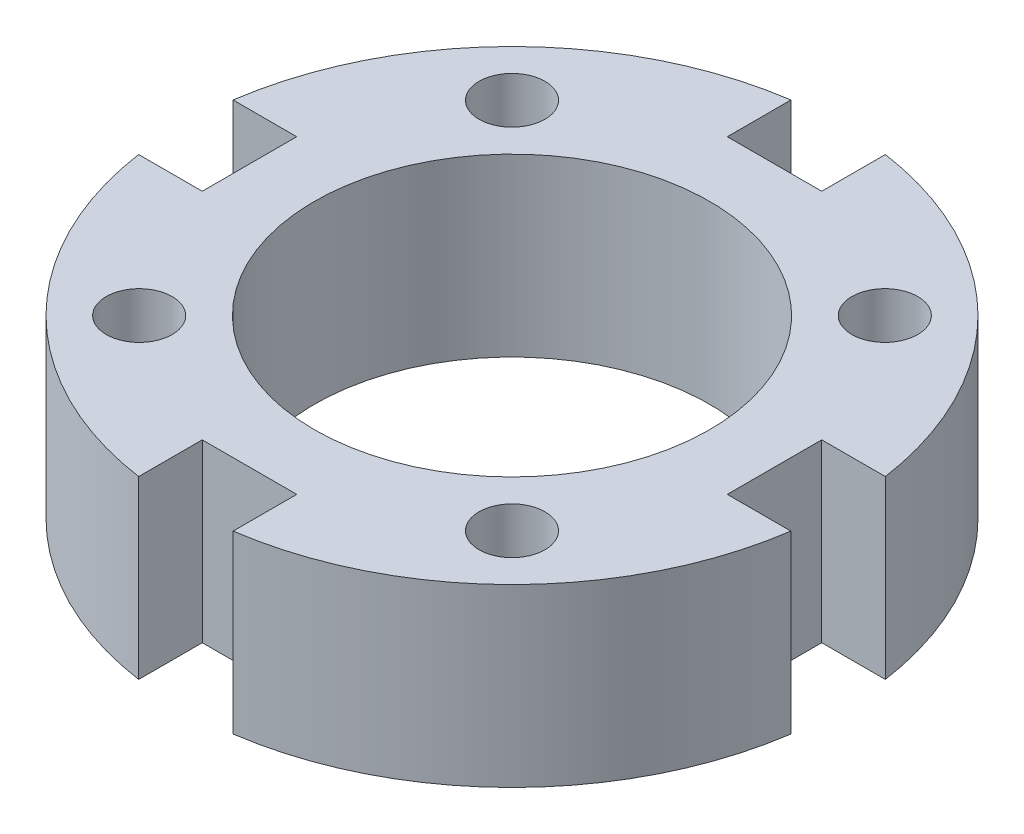
SolidWorks part; units mm, degrees
material "ABS"
ref_plane "Front Plane" through (0, 0, 0) normal (0, 0, 1) x (1, 0, 0)
ref_plane "Top Plane" through (0, 0, 0) normal (0, 1, 0) x (1, 0, 0)
ref_plane "Right Plane" through (0, 0, 0) normal (1, 0, 0) x (0, 0, -1)
sketch "Sketch1" plane through (0, 0, 0) normal (0, 1, 0) x (1, 0, 0)
  circle A0 centre (0, 0) radius 7.5
  circle A1 centre (0, 0) radius 4.5
  dimension "D1" = 15
  dimension "D2" = 3
extrude "Boss-Extrude1" add sketch "Sketch1" along normal blind 4 contours A0 | A1
sketch "Sketch2" plane through (0, 0, 0) normal (0, 0, 1) x (1, 0, 0)
  line L0 (0, 0) -> (0, -50000) construction
sketch "Sketch3" plane through (0, 0, 0) normal (1, 0, 0) x (0, 0, -1)
  line L0 (-7.5, 4) -> (0, 4) construction
  line L1 (0, 200000) -> (0, -250000) construction
  line L2 (0, 4) -> (0, 0)
  line L3 (0, 0) -> (-7.5, 0) construction
  line L4 (-7.5, 0) -> (-7.5, 4)
  line L6 (-7.5, 0) -> (-5.975, 0)
  line L7 (-5.975, 4) -> (-7.5, 4)
  line L15 (-5.975, 0) -> (-5.975, 4)
  point P14 (-8, 2)
  dimension "D4" = 1.525
  dimension "D1" = 7.5
extrude "Cut-Extrude1" cut sketch "Sketch3" against normal mid plane 2.15 contours L4 L7 L15 L6
pattern_circular "CirPattern1" count 4 over 360 about axis through (0, 0, 0) along (0, 1, 0) of "Cut-Extrude1"
sketch "Sketch6" plane through (0, 0, 0) normal (0, -1, 0) x (1, 0, 0)
  line L2 (0, 0) -> (5.3033, 5.3033) construction
  line L3 (0, 0) -> (0, -5.975)
  line L4 (0, 0) -> (4.2426, 4.2426)
  line L5 (1.075, -5.975) -> (-1.075, -5.975) construction
  line L6 (0, 0) -> (-5.975, 0)
  line L7 (-5.975, -1.075) -> (-5.975, 1.075) construction
  arc A0 (0, -8) -> (-8, 0) centre (0, 0) cw construction
  arc A1 (-7.4226, -1.075) -> (-1.075, -7.4226) centre (0, 0) ccw construction
  circle A2 centre (4.2426, 4.2426) radius 0.75
  dimension "D2" = 1.5
  dimension "D1" = 6
extrude "Cut-Extrude3" cut sketch "Sketch6" against normal through all contours A2
pattern_circular "CirPattern3" count 4 over 360 about axis through (0, 0, 0) along (0, 1, 0) of "Cut-Extrude3"
equation "\"D1@Sketch1\" = \"SpineDiameter\""
equation "\"D2@Sketch1\"=\"OuterThickness\""
equation "\"D1@Boss-Extrude1\" = \"DiscThickness\""
equation "\"D1@Cut-Extrude1\" = \"LigamentThickness\" + 0.15"
equation "\"D1@Sketch6\" = ( \"SpineDiameter\" - \"OuterThickness\" ) / 2"
equation "\"OuterThickness\"= 3mm"
equation "\"MasterFillet\"= 3mm"
equation "\"PartSeperation\"= 6mm"
equation "\"Tolerance\"= 0.15mm"
equation "\"D4@Sketch3\" = \"LigamentDepth\" + \"Tolerance\" + 0.375"
equation "\"D1@Sketch3\"= \"SpineDiameter\" / 2"
equation "\"HeightPart\"= 100mm"
equation "\"Holes\"= 1.5mm"
equation "\"SpineHolderThickness\"= 3mm"
equation "\"SpineHolderDepth\" = 3mm"
equation "\"DiscThickness\"= 4mm"
equation "\"LigamentThickness\"= 2mm"
equation "\"LigamentExtension\"= 1mm"
equation "\"LigamentAngle\"= 20deg"
equation "\"SpineDiameter\"= 15mm"
equation "\"LigamentDepth\"= 1mm"
equation "\"MotorLength\" = 40.5mm"
equation "\"MotorWidth\" = 20.3mm"
equation "\"AttachmentHeight\"= 3mm"
equation "\"SpoolDiameter\"= 60mm"
equation "\"SpoolHeight\"= 2mm"
equation "\"SpoolRidgeHeight\"= 1mm"
equation "\"SpoolRidgeDepth\"= 2mm"
equation "\"SpoolSeperation\"= 2mm"
equation "\"ServoHolderWidthOffset\"= 20mm"
equation "\"MotorTransmitterToScrew\"= 21.7mm"
equation "\"SpoolToSpine\"= 15mm"
equation "\"SpoolCenterToMotor\" = 31.5mm"
equation "\"HubOffset\"= 18mm"
equation "\"ServoFastenerHolders\"=2mm"
equation "\"ArduinoLength\" = 53.4mm"
equation "\"ArduinoWidth\" = 50mm"
equation "\"ArdYOffset\" = 29.5mm"
equation "\"ArdXOffset\" = 20.5mm"
equation "\"ArdXOffsetSmall\" = 25mm"
equation "\"MiddleServoOffset\"= 12mm"
equation "\"LargeServoOffset\"= 3mm"
equation "\"SmallServoOffset\"= 0mm"
equation "\"ToolHoleDiameter\"= 12mm"
